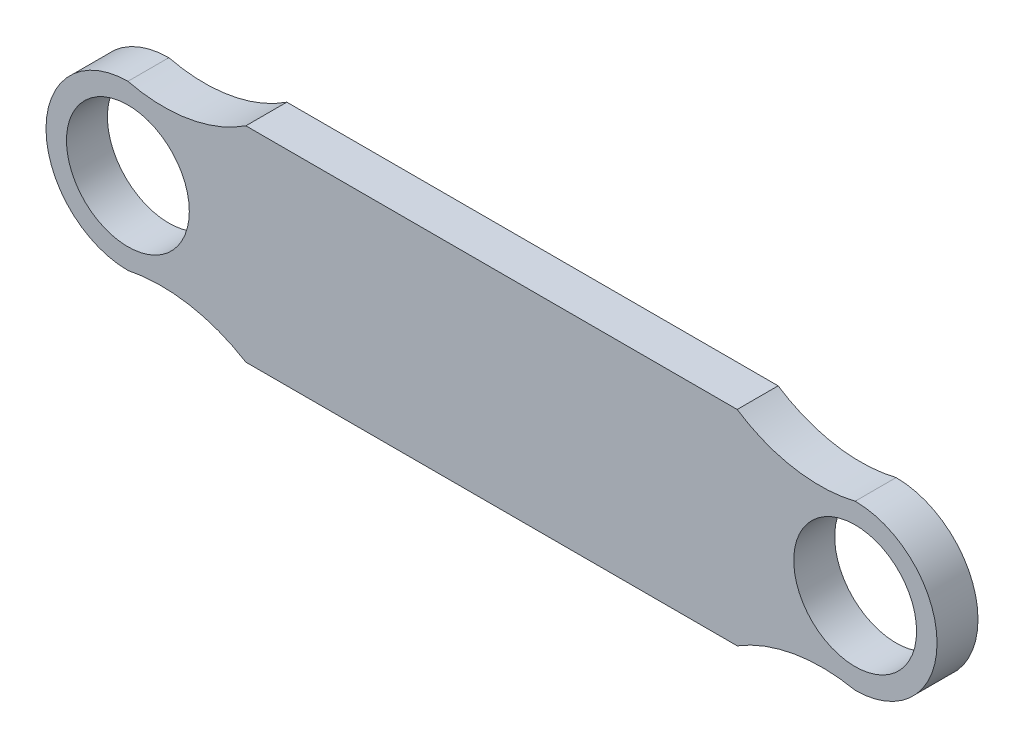
SolidWorks part; units mm, degrees
material "Cedar"
ref_plane "Front Plane" through (0, 0, 0) normal (0, 0, 1) x (1, 0, 0)
ref_plane "Top Plane" through (0, 0, 0) normal (0, 1, 0) x (1, 0, 0)
ref_plane "Right Plane" through (0, 0, 0) normal (1, 0, 0) x (0, 0, -1)
sketch "Sketch1" plane through (0, 0, 0) normal (0, 0, 1) x (1, 0, 0)
  line L0 (0, 5.7139) -> (0, -3.7119) construction
  line L1 (-18, -7.5) -> (18, -7.5)
  line L3 (-18, 7.5) -> (18, 7.5)
  line L5 (-18, -7.5) -> (18, 7.5) construction
  line L6 (-18, 7.5) -> (18, -7.5) construction
  circle A0 centre (26.6441, 0) radius 4.5
  arc A1 (25.0277, -5.7782) -> (24.8133, 5.7139) centre (26.6441, 0) ccw
  arc A2 (18, 7.5) -> (26.6441, 6) centre (24.0409, 16.6555) ccw
  arc A3 (18, -7.5) -> (26.6441, -6) centre (24.2182, -17.6771) cw
  arc A4 (-18, -7.5) -> (-26.6441, -6) centre (-24.2182, -17.6771) ccw
  arc A5 (-18, 7.5) -> (-26.6441, 6) centre (-24.0409, 16.6555) cw
  arc A6 (-25.0277, -5.7782) -> (-24.8133, 5.7139) centre (-26.6441, 0) cw
  circle A7 centre (-26.6441, 0) radius 4.5
  point P0 (0, 0)
  dimension "D3" = 12
  dimension "D4" = 9
  dimension "D1" = 36
  dimension "D2" = 15
extrude "Boss-Extrude1" add sketch "Sketch1" along normal blind 3 contours A6 A4 L1 A3 A1 A2 L3 A5 A0 A7
